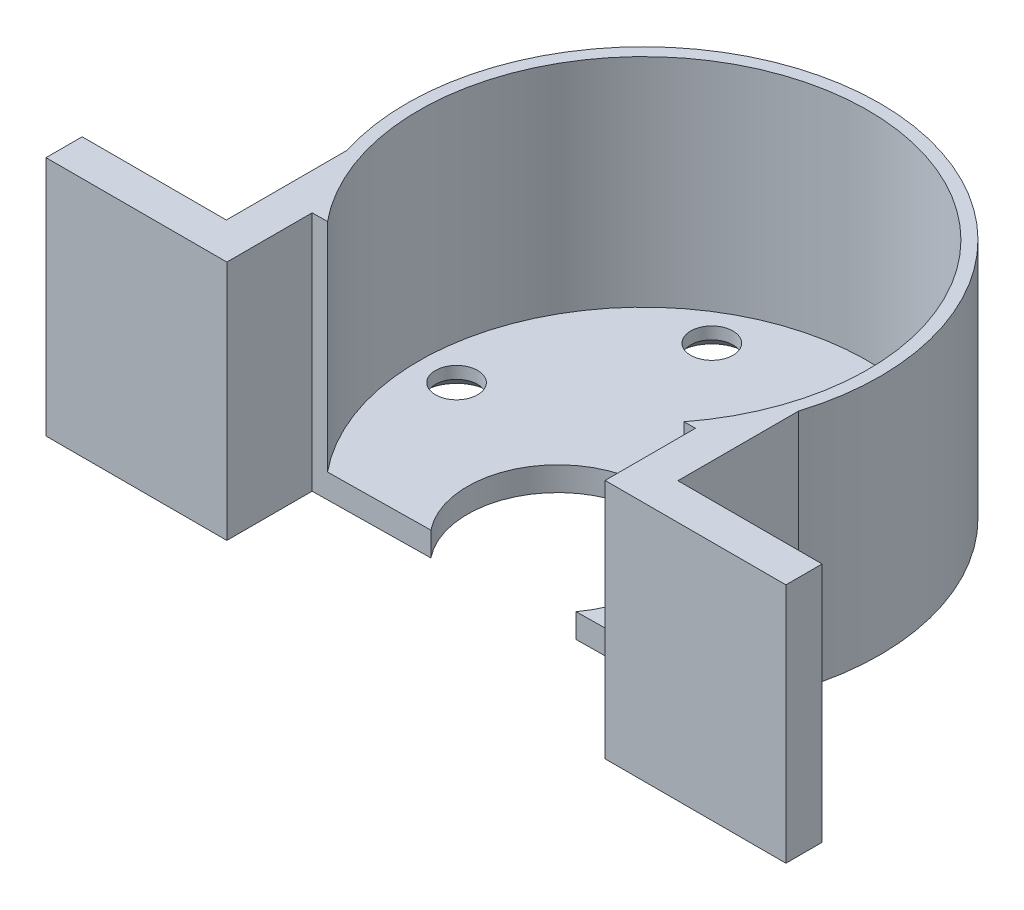
SolidWorks part; units mm, degrees
ref_plane "Front Plane" through (0, 0, 0) normal (0, 0, 1) x (1, 0, 0)
ref_plane "Top Plane" through (0, 0, 0) normal (0, 1, 0) x (1, 0, 0)
ref_plane "Right Plane" through (0, 0, 0) normal (1, 0, 0) x (0, 0, -1)
sketch "Sketch1" plane through (0, 0, 0) normal (0, 1, 0) x (1, 0, 0)
  line L1 (-15.687, -11.7923) -> (15.687, -11.3667)
  line L2 (30.687, -18.8658) -> (30.687, -15.8658)
  line L3 (-15.687, -11.7923) -> (15.687, -11.7923)
  line L5 (15.687, -11.7923) -> (15.687, -14.2855)
  line L6 (-18.7279, -15.8658) -> (-30.687, -15.8658)
  line L7 (-18.7279, -5.8658) -> (22.8479, -5.8658) construction
  line L8 (0, 0) -> (0, -21.9335) construction
  line L12 (-15.687, -11.7923) -> (-15.687, -14.2855)
  line L13 (15.687, -14.2855) -> (15.687, -18.8658)
  line L14 (-30.687, -18.8658) -> (-15.687, -18.8658)
  line L16 (-30.687, -15.8658) -> (-30.687, -18.8658)
  line L18 (-15.687, -14.2855) -> (-15.687, -18.8658)
  line L19 (30.687, -18.8658) -> (15.687, -18.8658)
  line L21 (15.687, -11.7923) -> (15.687, -11.3667)
  line L22 (-18.7279, -15.8658) -> (-18.7279, -5.8658)
  line L23 (18.7279, -5.8658) -> (18.7279, -15.8658)
  line L24 (18.7279, -15.8658) -> (30.687, -15.8658)
  circle A2 centre (0, 0) radius 19.625
  dimension "D2" = 10
  dimension "D3" = 3
  dimension "D1" = 39.25
  dimension "D4" = 90.777
  dimension "D5" = 3
  dimension "D6" = 15
extrude "Boss-Extrude2" add sketch "Sketch1" along normal blind 20
sketch "Sketch3" plane through (0, 20, 0) normal (0, 1, 0) x (1, 0, 0)
  line L0 (0, 0) -> (0, 28.072) construction
  circle A0 centre (0, 0) radius 18.625
  dimension "D1" = 37.25
extrude "Cut-Extrude1" cut sketch "Sketch3" against normal blind 18 contours A0
sketch "Sketch5" plane through (0, 2, 0) normal (0, 1, 0) x (1, 0, 0)
  line L1 (-0.2526, 18.6233) -> (0.157, -11.5774) construction
  line L2 (-14.4303, -11.7753) -> (14.7444, -11.3795) construction
  line L3 (18.625, 0) -> (-18.625, 0) construction
  arc A0 (14.7444, -11.3795) -> (-14.4303, -11.7753) centre (0, 0) ccw construction
  circle A2 centre (-0.095, -7) radius 7.5
  dimension "D1" = 15
extrude "Cut-Extrude2" cut sketch "Sketch5" against normal blind 2
sketch "Sketch6" plane through (0, 0, 0) normal (0, -1, 0) x (-1, 0, 0)
  line L0 (0, 0) -> (-9.8125, 16.9957) construction
  line L1 (0, 19.625) -> (0, -16.0596) construction
  line L2 (-19.625, 0) -> (19.625, 0) construction
  arc A0 (18.7279, -5.8658) -> (-18.7279, -5.8658) centre (0, 0) ccw construction
  circle A1 centre (0, 0) radius 15.5
  dimension "D1" = 31
  dimension "D2" = 30
sketch "Sketch8" plane through (0, 0, 0) normal (0, -1, 0) x (-1, 0, 0)
  line L0 (0, 0) -> (-9.8125, 16.9957) construction
  circle A0 centre (-7.75, 13.4234) radius 1.8957
  circle A1 centre (0, 0) radius 15.5 construction
  circle A2 centre (7.75, 13.4234) radius 1.8957
  circle A3 centre (15.5, 0) radius 1.8957
  circle A4 centre (7.75, -13.4234) radius 1.8957
  circle A5 centre (-7.75, -13.4234) radius 1.8957
  circle A6 centre (-15.5, 0) radius 1.8957
  point P19 (0, 0)
  dimension "D1" = 6
hole_wizard "CSK for M3 Countersunk Flat Head Screw2" positions "3DSketch2" profile "Sketch9" countersink size "M3" standard "ISO" end condition through all
sketch3d "3DSketch2"
  point P0 (7.75, 0, -13.4234)
  point P3 (-7.75, 0, -13.4234)
  point P6 (-15.5, 0, 0)
  point P9 (15.5, 0, 0)
sketch "Sketch9" plane through (7.75, 0, -13.4234) normal (1, 0, 0) x (0, 0, -1)
  line L0 (0, 0) -> (0, 20)
  line L1 (0, 20) -> (1.75, 20)
  line L2 (1.75, 20) -> (1.75, 1)
  line L3 (1.75, 1) -> (2.75, 0)
  line L5 (2.75, 0) -> (0, 0)
  line L6 (-1.75, 1) -> (-2.75, 0) construction
  line L11 (0, -6.35) -> (0, 107.95) construction
  dimension "Thru Hole Dia." = 3.5
  dimension "Thru Hole Depth" = 20
  dimension "Near C'Sink Dia." = 5.5
  dimension "Near C'Sink Angle" = 90
